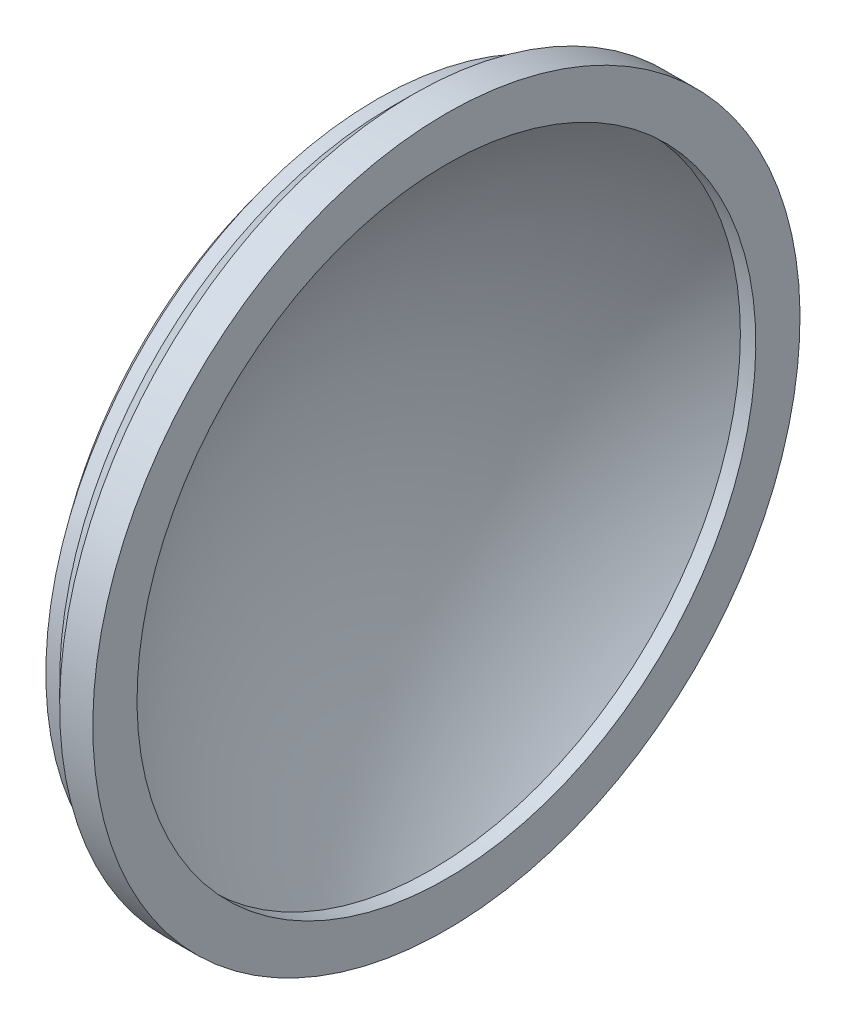
SolidWorks part; units mm, degrees
ref_plane "Front Plane" through (0, 0, 0) normal (0, 0, 1) x (1, 0, 0)
ref_plane "Top Plane" through (0, 0, 0) normal (0, 1, 0) x (1, 0, 0)
ref_plane "Right Plane" through (0, 0, 0) normal (1, 0, 0) x (0, 0, -1)
sketch "Sketch1" plane through (0, 0, 0) normal (0, 0, 1) x (1, 0, 0)
  line L4 (-16, 64) -> (-16, 56)
  line L5 (-16, 64) -> (-22, 64)
  line L6 (-22, 64) -> (-26, 60)
  line L7 (-26, 60) -> (-28.5, 60)
  line L8 (-39.8454, 0) -> (-49.8454, 0)
  line L9 (-16, 56) -> (-18.7907, 56)
  line L10 (0, 0) -> (-24.6575, 0) construction
  arc A1 (-18.7907, 56) -> (-39.8454, 0) centre (45.1546, 0) ccw
  arc A2 (-28.5, 60) -> (-49.8454, 0) centre (45.1546, 0) ccw
  dimension "D5" = 8
  dimension "D7" = 190
  dimension "D8" = 170
  dimension "D9" = 64
  dimension "D1" = 6
  dimension "D2" = 2.5
  dimension "D3" = 135
  dimension "D4" = 4
  dimension "D6" = 16
revolve "Revolve1" add sketch "Sketch1" angle 360 about L10
